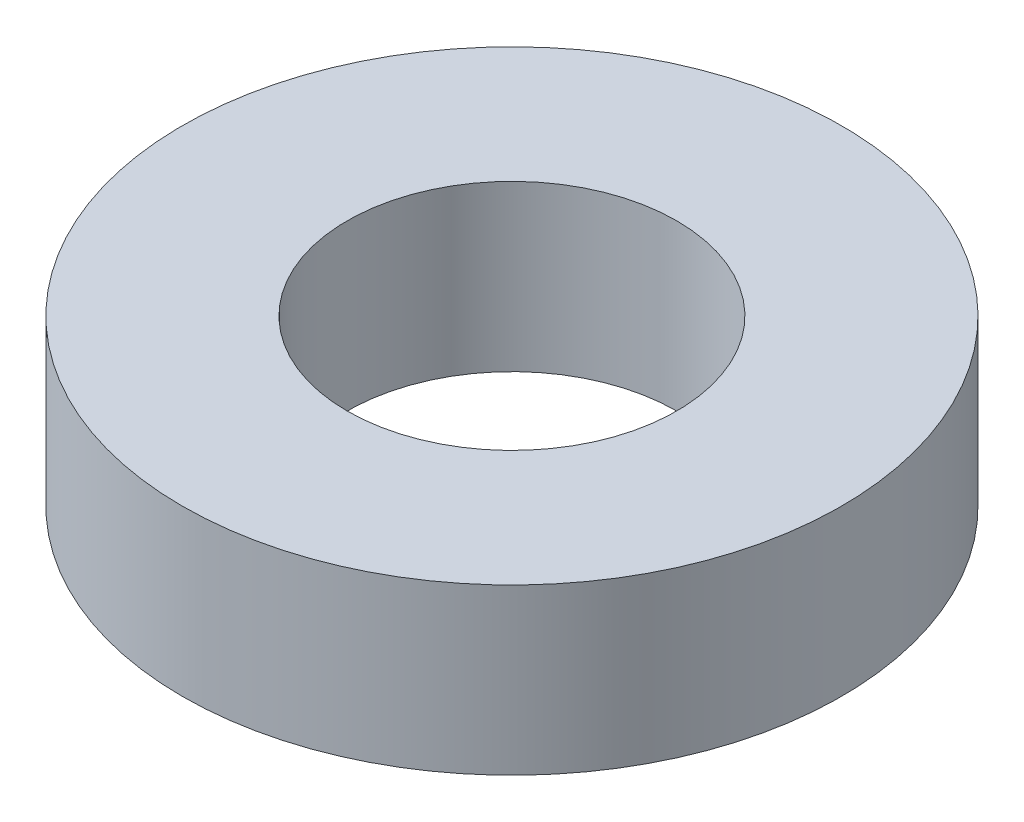
SolidWorks part; units mm, degrees
ref_plane "Front Plane" through (0, 0, 0) normal (0, 0, 1) x (1, 0, 0)
ref_plane "Top Plane" through (0, 0, 0) normal (0, 1, 0) x (1, 0, 0)
ref_plane "Right Plane" through (0, 0, 0) normal (1, 0, 0) x (0, 0, -1)
sketch "Sketch1" plane through (0, 0, 0) normal (0, 1, 0) x (1, 0, 0)
  circle A0 centre (0, 0) radius 2
  circle A1 centre (0, 0) radius 4
  dimension "D1" = 8
  dimension "D2" = 4
extrude "Boss-Extrude1" add sketch "Sketch1" along normal blind 2
